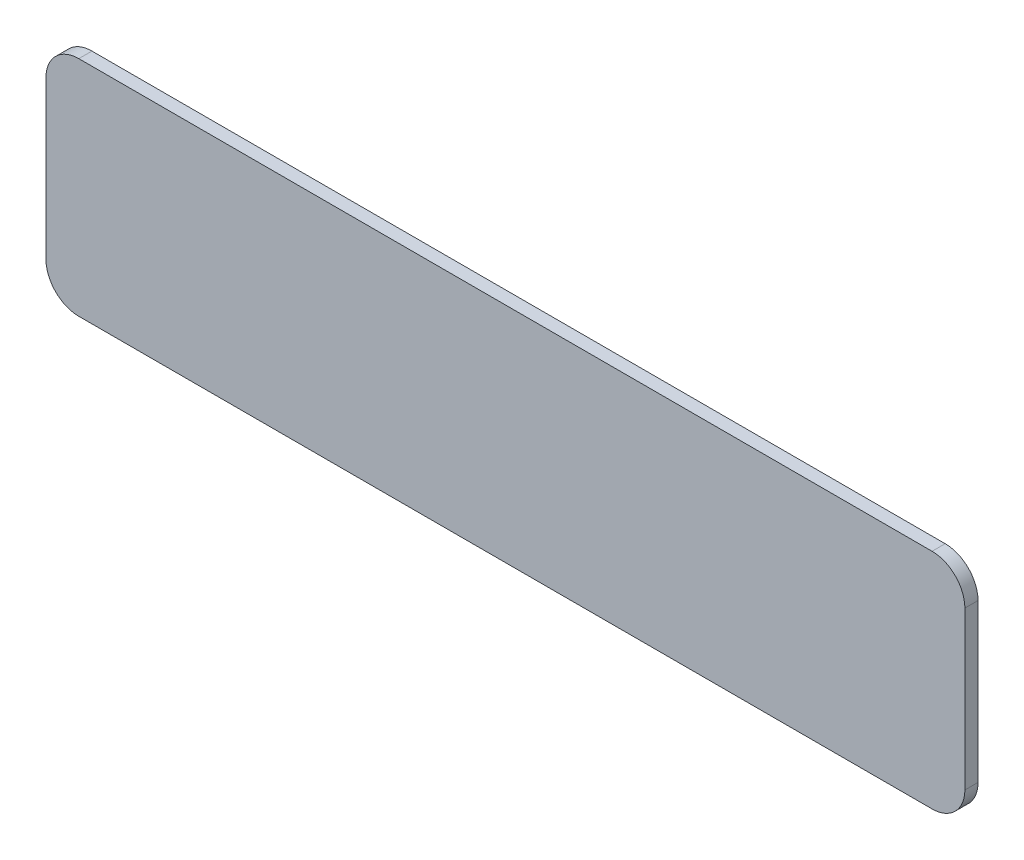
SolidWorks part; units mm, degrees
ref_plane "Front Plane" through (0, 0, 0) normal (0, 0, 1) x (1, 0, 0)
ref_plane "Top Plane" through (0, 0, 0) normal (0, 1, 0) x (1, 0, 0)
ref_plane "Right Plane" through (0, 0, 0) normal (1, 0, 0) x (0, 0, -1)
sketch "Sketch1" plane through (0, 0, 0) normal (0, 0, 1) x (1, 0, 0)
  line L1 (-65, 17) -> (65, 17)
  line L2 (-70, 12) -> (-70, -12)
  line L3 (-65, -17) -> (65, -17)
  line L4 (70, 12) -> (70, -12)
  line L5 (-70, 17) -> (70, -17) construction
  line L6 (-70, -17) -> (70, 17) construction
  arc A0 (65, 17) -> (70, 12) centre (65, 12) cw
  arc A1 (70, -12) -> (65, -17) centre (65, -12) cw
  arc A2 (-65, -17) -> (-70, -12) centre (-65, -12) cw
  arc A3 (-70, 12) -> (-65, 17) centre (-65, 12) cw
  point P0 (0, 0)
  dimension "D3" = 5
  dimension "D1" = 34
  dimension "D2" = 140
extrude "Boss-Extrude1" add sketch "Sketch1" along normal blind 2
